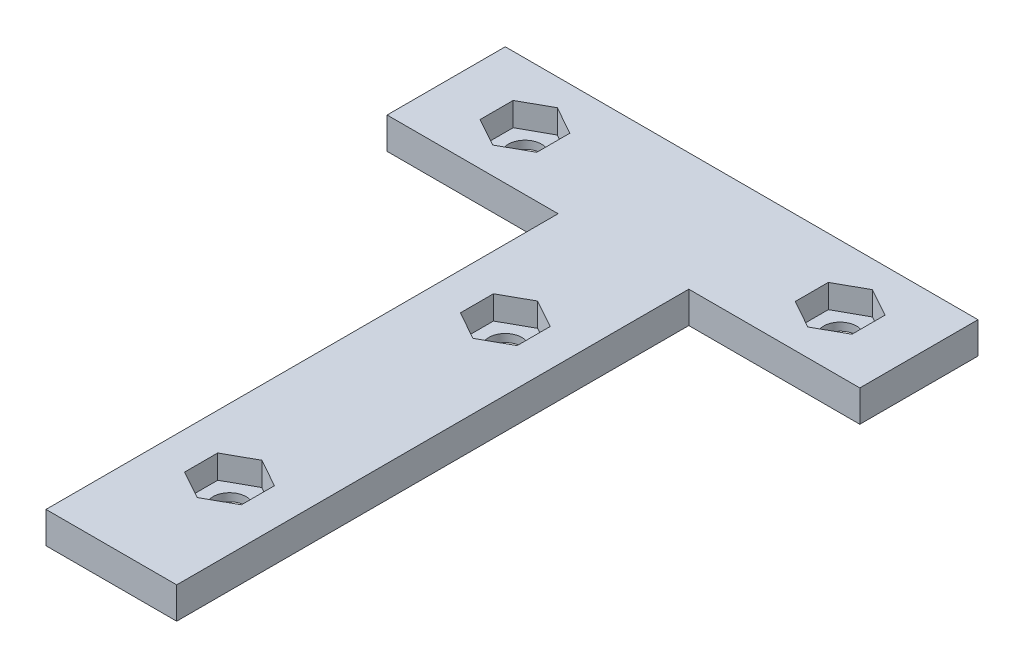
SolidWorks part; units mm, degrees
ref_plane "Front Plane" through (0, 0, 0) normal (0, 0, 1) x (1, 0, 0)
ref_plane "Top Plane" through (0, 0, 0) normal (0, 1, 0) x (1, 0, 0)
ref_plane "Right Plane" through (0, 0, 0) normal (1, 0, 0) x (0, 0, -1)
sketch "Sketch2" plane through (0, 0, 0) normal (0, 1, 0) x (1, 0, 0)
  line L1 (9.4484, -267.3604) -> (69.4484, -267.3604)
  line L2 (9.4484, -267.3604) -> (9.4484, -282.3604)
  line L3 (9.4484, -282.3604) -> (69.4484, -282.3604)
  line L4 (69.4484, -267.3604) -> (69.4484, -282.3604)
  line L5 (31.1541, -282.3604) -> (47.7427, -282.3604)
  line L6 (31.1541, -282.3604) -> (31.1541, -347.3604)
  line L7 (31.1541, -347.3604) -> (47.7427, -347.3604)
  line L8 (47.7427, -282.3604) -> (47.7427, -347.3604)
  circle A0 centre (19.4484, -274.8604) radius 2.1
  circle A1 centre (59.4484, -274.8604) radius 2.1
  circle A2 centre (39.4484, -297.3604) radius 2.1
  circle A3 centre (39.4484, -332.3604) radius 2.1
sketch "Sketch3" plane through (0, 0, 0) normal (0, 1, 0) x (1, 0, 0)
  line L1 (9.4484, -267.3604) -> (69.4484, -267.3604)
  line L2 (9.4484, -267.3604) -> (9.4484, -282.3604)
  line L3 (9.4484, -282.3604) -> (69.4484, -282.3604)
  line L4 (69.4484, -267.3604) -> (69.4484, -282.3604)
  line L5 (31.1541, -347.3604) -> (47.7427, -347.3604)
  line L6 (31.1541, -347.3604) -> (31.1541, -282.3604)
  line L7 (31.1541, -282.3604) -> (47.7427, -282.3604)
  line L8 (47.7427, -347.3604) -> (47.7427, -282.3604)
  circle A0 centre (19.4484, -274.8604) radius 2.1
  circle A1 centre (59.4484, -274.8604) radius 2.1
  circle A2 centre (39.4484, -297.3604) radius 2.1
  circle A3 centre (39.4484, -332.3604) radius 2.1
extrude "Boss-Extrude1" add sketch "Sketch3" along normal blind 4 contours L5 L8 L3 L6 A3 A2 | L4 L1 L2 L3 A1 A0
sketch "Sketch4" plane through (0, 4, 0) normal (0, 1, 0) x (1, 0, 0)
  line L0 (19.4484, -272.7604) -> (19.4484, -270.7604) construction
  line L2 (15.8484, -276.9604) -> (15.8484, -272.7604)
  line L4 (23.0484, -276.9604) -> (23.0484, -272.7604)
  line L5 (39.4484, -267.3604) -> (39.4484, -273.384) construction
  line L6 (19.4484, -270.7604) -> (15.8484, -272.7604)
  line L7 (23.0484, -272.7604) -> (19.4484, -270.7604)
  line L8 (23.0484, -276.9604) -> (19.4484, -278.9604)
  line L9 (19.4484, -278.9604) -> (15.8484, -276.9604)
  line L10 (9.4484, -267.3604) -> (69.4484, -267.3604) construction
  line L11 (55.8484, -276.9604) -> (55.8484, -272.7604)
  line L12 (55.8484, -276.9604) -> (59.4484, -278.9604)
  line L13 (59.4484, -278.9604) -> (63.0484, -276.9604)
  line L14 (63.0484, -276.9604) -> (63.0484, -272.7604)
  line L15 (59.4484, -270.7604) -> (63.0484, -272.7604)
  line L16 (55.8484, -272.7604) -> (59.4484, -270.7604)
  point P0 (19.4484, -274.8604)
  dimension "D1" = 7.2
  dimension "D2" = 4.2
  dimension "D3" = 2
extrude "Cut-Extrude1" cut sketch "Sketch4" against normal blind 3
sketch "Sketch5" plane through (0, 4, 0) normal (0, 1, 0) x (1, 0, 0)
  line L0 (35.8484, -297.3604) -> (43.0484, -297.3604) construction
  line L1 (39.4484, -314.8604) -> (47.7427, -314.8604) construction
  line L2 (47.7427, -347.3604) -> (47.7427, -282.3604) construction
  line L3 (39.4484, -301.4604) -> (43.0484, -299.4604)
  line L5 (35.8484, -299.4604) -> (35.8484, -295.2604)
  line L7 (43.0484, -299.4604) -> (43.0484, -295.2604)
  line L8 (39.4484, -301.4604) -> (35.8484, -299.4604)
  line L9 (39.4484, -328.2604) -> (35.8484, -330.2604)
  line L10 (39.4484, -293.2604) -> (35.8484, -295.2604)
  line L11 (39.4484, -293.2604) -> (43.0484, -295.2604)
  line L12 (39.4484, -328.2604) -> (43.0484, -330.2604)
  line L13 (39.4484, -314.8604) -> (39.4484, -332.3604) construction
  line L14 (43.0484, -330.2604) -> (43.0484, -334.4604)
  line L15 (39.4484, -336.4604) -> (43.0484, -334.4604)
  line L16 (39.4484, -336.4604) -> (35.8484, -334.4604)
  line L17 (35.8484, -330.2604) -> (35.8484, -334.4604)
  dimension "D1" = 4.2
  dimension "D2" = 7.2
extrude "Cut-Extrude2" cut sketch "Sketch5" against normal blind 3
